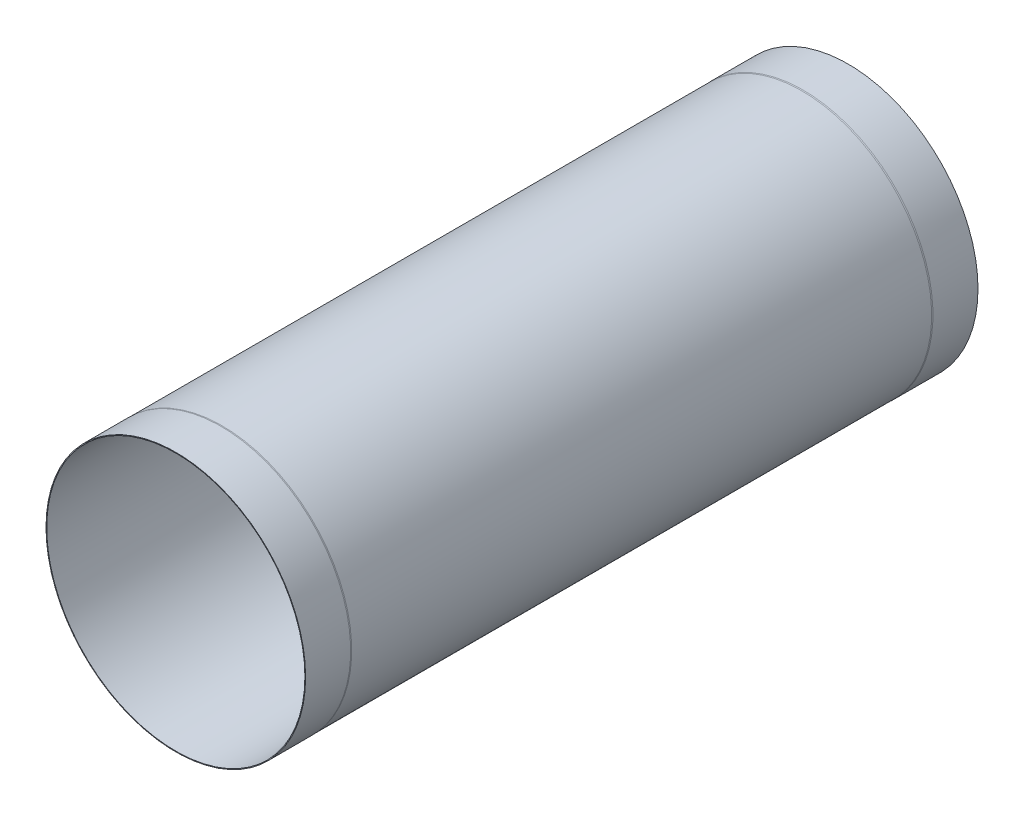
SolidWorks part; units mm, degrees
material "Thornel Mat VMA"
ref_plane "Front Plane" through (0, 0, 0) normal (0, 0, 1) x (1, 0, 0)
ref_plane "Top Plane" through (0, 0, 0) normal (0, 1, 0) x (1, 0, 0)
ref_plane "Right Plane" through (0, 0, 0) normal (1, 0, 0) x (0, 0, -1)
sketch "Sketch1" plane through (0, 0, 0) normal (0, 0, 1) x (1, 0, 0)
  circle A0 centre (0, 0) radius 216.126
  circle A1 centre (0, 0) radius 214.95
  dimension "D2" = 429.9
  dimension "D1" = 1.176
extrude "Extrude1" add sketch "Sketch1" along normal mid plane 1119.6
sketch "Sketch2" plane through (0, 0, 0) normal (0, 1, 0) x (1, 0, 0)
  line L0 (216.126, 484.8) -> (215.905, 482.8)
  line L1 (216.126, -559.8) -> (216.126, 559.8) construction
  line L2 (215.905, 482.8) -> (215.905, -482.8)
  line L3 (215.905, -482.8) -> (216.126, -484.8)
  line L4 (216.126, -484.8) -> (216.126, 484.8)
  line L5 (0, 624.558) -> (0, -745.0198) construction
  line L7 (214.95, -559.8) -> (214.95, 559.8) construction
  line L8 (0, 0) -> (215.905, 0) construction
  line L9 (215.905, 0) -> (216.126, 0) construction
  line L10 (216.126, 559.8) -> (-216.126, 559.8) construction
  dimension "D1" = 0.955
  dimension "D2" = 75
  dimension "D3" = 2
revolve "Cut-Revolve1" cut sketch "Sketch2" angle 360 about L5
